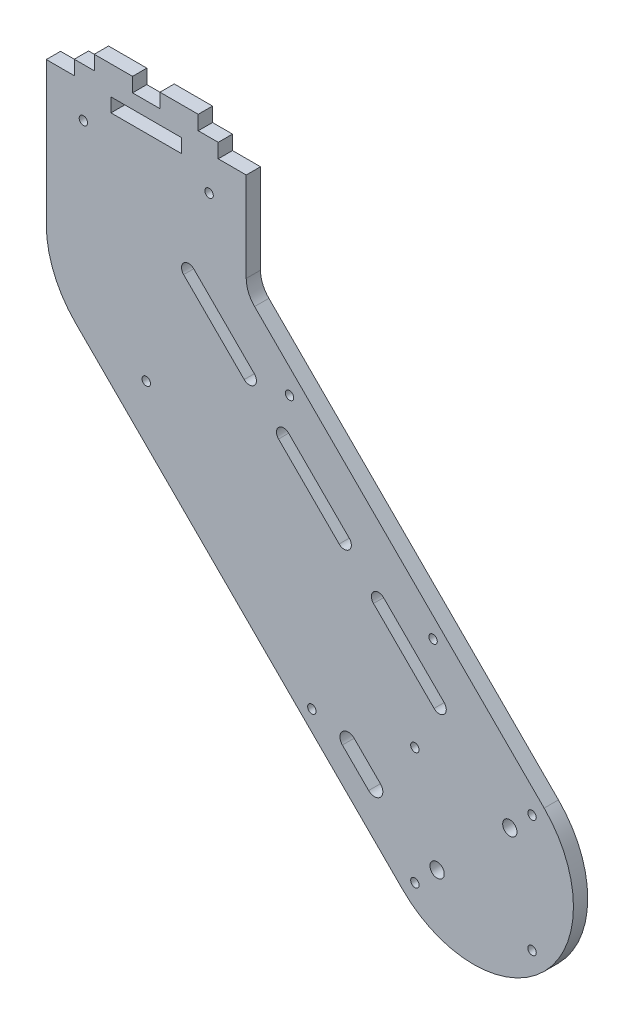
SolidWorks part; units mm, degrees
ref_plane "Front Plane" through (0, 0, 0) normal (0, 0, 1) x (1, 0, 0)
ref_plane "Top Plane" through (0, 0, 0) normal (0, 1, 0) x (1, 0, 0)
ref_plane "Right Plane" through (0, 0, 0) normal (1, 0, 0) x (0, 0, -1)
sketch "Sketch1" plane through (0, 0, 0) normal (0, 0, 1) x (1, 0, 0)
  line L0 (0, 0) -> (35, 0) construction
  line L1 (0, 0) -> (0, 35) construction
  line L2 (0, 0) -> (24.7487, 24.7487) construction
  line L3 (0, 0) -> (-24.7487, -24.7487) construction
  line L4 (-24.7487, -24.7487) -> (-139.3, 89.8026)
  line L5 (0, 0) -> (24.7487, -24.7487) construction
  line L6 (-139.3, 89.8026) -> (-114.5513, 114.5513) construction
  line L7 (24.7487, 24.7487) -> (-54.6728, 104.1703)
  line L8 (-43.834, 10.6132) -> (-34.6417, 1.4208) construction
  line L11 (-114.5513, 114.5513) -> (0, 0) construction
  line L12 (-41.7764, 12.6709) -> (-32.584, 3.4785)
  line L15 (-31.8198, 38.8909) -> (-10.6066, 60.1041) construction
  line L16 (-45.8917, 8.5555) -> (-36.6993, -0.6369)
  line L19 (-31.8198, 38.8909) -> (-60.1041, 10.6066) construction
  line L20 (-33.234, 58.6899) -> (-12.0208, 37.4767) construction
  line L26 (-64.3969, 105.3087) -> (-109.6016, 60.1041) construction
  line L30 (-31.4663, 60.4576) -> (-10.253, 39.2444)
  line L33 (-74.2462, 74.2462) -> (-49.4975, 98.9949) construction
  line L34 (-70.3571, 70.3571) -> (-45.6084, 95.1059) construction
  line L37 (-35.0018, 56.9221) -> (-13.7886, 35.7089)
  line L40 (-114.5513, 114.5513) -> (-207.3962, 114.5513) construction
  line L41 (-149.5513, 114.5513) -> (-149.5513, 164.5513)
  line L42 (-114.5513, 114.5513) -> (-8.6743, 114.5513) construction
  line L43 (-79.5513, 133.1909) -> (-79.5513, 165.6653)
  line L44 (-114.5513, 114.5513) -> (-79.5513, 149.5513) construction
  line L45 (-54.6728, 104.1703) -> (-76.6224, 126.1198)
  line L46 (-114.5513, 114.5513) -> (-146.8871, 101.1574) construction
  line L47 (-146.8871, 101.1574) -> (-49.8797, 141.3391) construction
  line L48 (-114.5513, 114.5513) -> (-114.5513, 83.0763) construction
  line L49 (-132.7513, 174.5513) -> (-119.3513, 174.5513) construction
  line L50 (-79.5513, 165.6653) -> (-79.5513, 174.5513)
  line L51 (-119.3513, 169.5513) -> (-109.7513, 169.5513)
  line L52 (-114.5513, 114.5513) -> (-114.5513, 174.5513) construction
  line L53 (-119.3513, 174.5513) -> (-132.7513, 174.5513)
  line L54 (-126.9013, 164.5513) -> (-102.2013, 164.5513)
  line L55 (-126.9013, 164.5513) -> (-126.9013, 159.7013)
  line L56 (-126.9013, 159.7013) -> (-102.2013, 159.7013)
  line L57 (-102.2013, 164.5513) -> (-102.2013, 159.7013)
  line L58 (-139.7513, 169.5513) -> (-132.7513, 169.5513) construction
  line L59 (-66.468, 91.9239) -> (-45.2548, 70.7107) construction
  line L60 (-132.7513, 174.5513) -> (-132.7513, 169.5513) construction
  line L61 (-119.3513, 169.5513) -> (-119.3513, 174.5513)
  line L62 (-114.5513, 174.5513) -> (-96.3513, 174.5513) construction
  line L63 (-114.5513, 159.7013) -> (-114.5513, 164.5513) construction
  line L64 (-126.9013, 162.1263) -> (-102.2013, 162.1263) construction
  line L65 (-149.5513, 164.5513) -> (-79.5513, 164.5513) construction
  line L66 (-132.7513, 169.5513) -> (-139.7513, 169.5513)
  line L67 (-139.7513, 169.5513) -> (-139.7513, 164.5513)
  line L68 (-139.7513, 164.5513) -> (-149.5513, 164.5513)
  line L69 (-132.7513, 169.5513) -> (-132.7513, 174.5513)
  line L70 (-109.7513, 169.5513) -> (-109.7513, 174.5513)
  line L71 (-109.7513, 174.5513) -> (-96.3513, 174.5513)
  line L72 (-96.3513, 169.5513) -> (-96.3513, 174.5513)
  line L73 (-96.3513, 169.5513) -> (-89.3513, 169.5513)
  line L74 (-89.3513, 169.5513) -> (-89.3513, 164.5513)
  line L75 (-89.3513, 164.5513) -> (-79.5513, 164.5513)
  line L76 (-119.3513, 169.5513) -> (-109.7513, 169.5513) construction
  line L77 (-96.3513, 169.5513) -> (-89.3513, 169.5513) construction
  line L78 (-64.7003, 93.6916) -> (-43.4871, 72.4784)
  line L79 (-68.2358, 90.1561) -> (-47.0226, 68.9429)
  line L80 (-99.7021, 125.1579) -> (-78.4889, 103.9447) construction
  line L81 (-97.9343, 126.9257) -> (-76.7211, 105.7125)
  line L82 (-101.4698, 123.3901) -> (-80.2566, 102.1769)
  arc A1 (-24.7487, -24.7487) -> (24.7487, 24.7487) centre (0, 0) ccw
  circle A3 centre (20.5061, -20.5061) radius 1.475
  circle A4 centre (-20.5061, -20.5061) radius 1.475
  circle A5 centre (-20.5061, 20.5061) radius 1.475
  circle A6 centre (20.5061, 20.5061) radius 1.475
  circle A15 centre (-14.1421, 56.5685) radius 1.475
  circle A16 centre (-56.5685, 14.1421) radius 1.475
  circle A17 centre (-64.3969, 105.3087) radius 1.475
  arc A29 (-149.5513, 114.5513) -> (-139.3, 89.8026) centre (-114.5513, 114.5513) ccw
  arc A31 (-76.6224, 126.1198) -> (-79.5513, 133.1909) centre (-69.5513, 133.1909) cw
  circle A36 centre (-114.5513, 84.5513) radius 1.475
  circle A37 centre (-136.5513, 152.5513) radius 1.475
  circle A38 centre (-92.5513, 152.5513) radius 1.475
  circle A43 centre (12.7279, 12.7279) radius 2.5
  circle A44 centre (-12.7279, -12.7279) radius 2.5
  arc A45 (-41.7764, 12.6709) -> (-45.8917, 8.5555) centre (-43.834, 10.6132) ccw
  arc A46 (-36.6993, -0.6369) -> (-32.584, 3.4785) centre (-34.6417, 1.4208) ccw
  arc A49 (-31.4663, 60.4576) -> (-35.0018, 56.9221) centre (-33.234, 58.6899) ccw
  arc A50 (-13.7886, 35.7089) -> (-10.253, 39.2444) centre (-12.0208, 37.4767) ccw
  arc A51 (-64.7003, 93.6916) -> (-68.2358, 90.1561) centre (-66.468, 91.9239) ccw
  arc A52 (-47.0226, 68.9429) -> (-43.4871, 72.4784) centre (-45.2548, 70.7107) ccw
  arc A53 (-97.9343, 126.9257) -> (-101.4698, 123.3901) centre (-99.7021, 125.1579) ccw
  arc A54 (-80.2566, 102.1769) -> (-76.7211, 105.7125) centre (-78.4889, 103.9447) ccw
  point P23 (0, 0)
  point P24 (-39.2378, 6.017)
  point P31 (-22.6274, 48.0833)
  point P40 (-55.8614, 81.3173)
  point P46 (-89.0955, 114.5513)
  point P107 (-79.5513, 129.0488)
  point P123 (-114.5513, 162.1263)
  dimension "D2" = 70
  dimension "D7" = 2.95
  dimension "D12" = 2.91
  dimension "D15" = 2.5
  dimension "D20" = 2.95
  dimension "D22" = 2.95
  dimension "D25" = 30
  dimension "D29" = 17
  dimension "D30" = 2.5
  dimension "D35" = 35.1835
  dimension "D36" = 32.1163
  dimension "D37" = 10
  dimension "D41" = 2.95
  dimension "D43" = 2.95
  dimension "D61" = 18
  dimension "D62" = 5
  dimension "D14" = 30
  dimension "D26" = 2.5
  dimension "D3" = 45
  dimension "D4" = 180
  dimension "D5" = 162
  dimension "D8" = 29
  dimension "D10" = 35
  dimension "D11" = 25.5
  dimension "D13" = 13
  dimension "D16" = 35
  dimension "D17" = 18
  dimension "D18" = 18
  dimension "D19" = 17
  dimension "D21" = 5
  dimension "D23" = 6.071
  dimension "D24" = 70
  dimension "D27" = 18
  dimension "D28" = 30
  dimension "D32" = 70
  dimension "D33" = 35
  dimension "D34" = 180
  dimension "D42" = 30
  dimension "D44" = 13
  dimension "D45" = 38
  dimension "D47" = 18.2
  dimension "D48" = 12.425
  dimension "D49" = 10
  dimension "D50" = 24.7
  dimension "D51" = 5
  dimension "D52" = 13.4
  dimension "D53" = 5
  dimension "D54" = 25.2
  dimension "D9" = 4
extrude "Boss-Extrude1" add sketch "Sketch1" against normal blind 5
